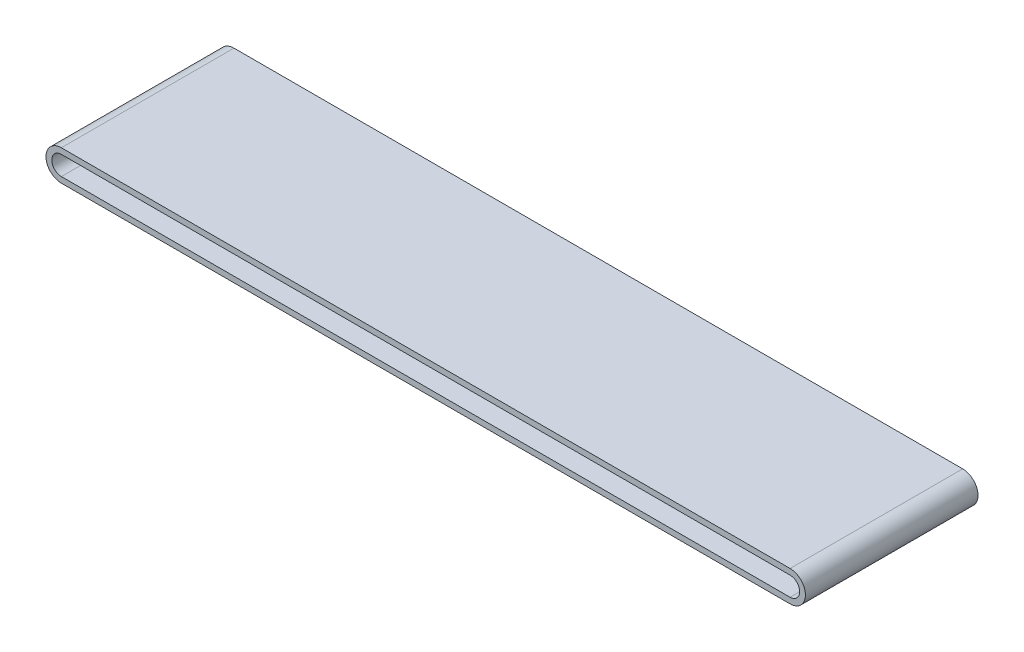
SolidWorks part; units mm, degrees
ref_plane "前视基准面" through (0, 0, 0) normal (0, 0, 1) x (1, 0, 0)
ref_plane "上视基准面" through (0, 0, 0) normal (0, 1, 0) x (1, 0, 0)
ref_plane "右视基准面" through (0, 0, 0) normal (1, 0, 0) x (0, 0, -1)
other "Configuration Table"
sketch "草图2" plane through (0, 0, 0) normal (0, 0, 1) x (1, 0, 0)
  line L0 (0, 0) -> (1, 0) construction
  line L1 (0, 0) -> (0, 1) construction
  line L2 (2.4781, 5) -> (382.4781, 5)
  line L3 (382.4781, -5) -> (2.4781, -5)
  arc A0 (2.4781, -5) -> (2.4781, 5) centre (2.4781, 0) cw
  arc A1 (382.4781, 5) -> (382.4781, -5) centre (382.4781, 0) cw
extrude "拉伸-薄壁1" add sketch "草图2" along normal mid plane 90 thin thin type one direction wall 3
